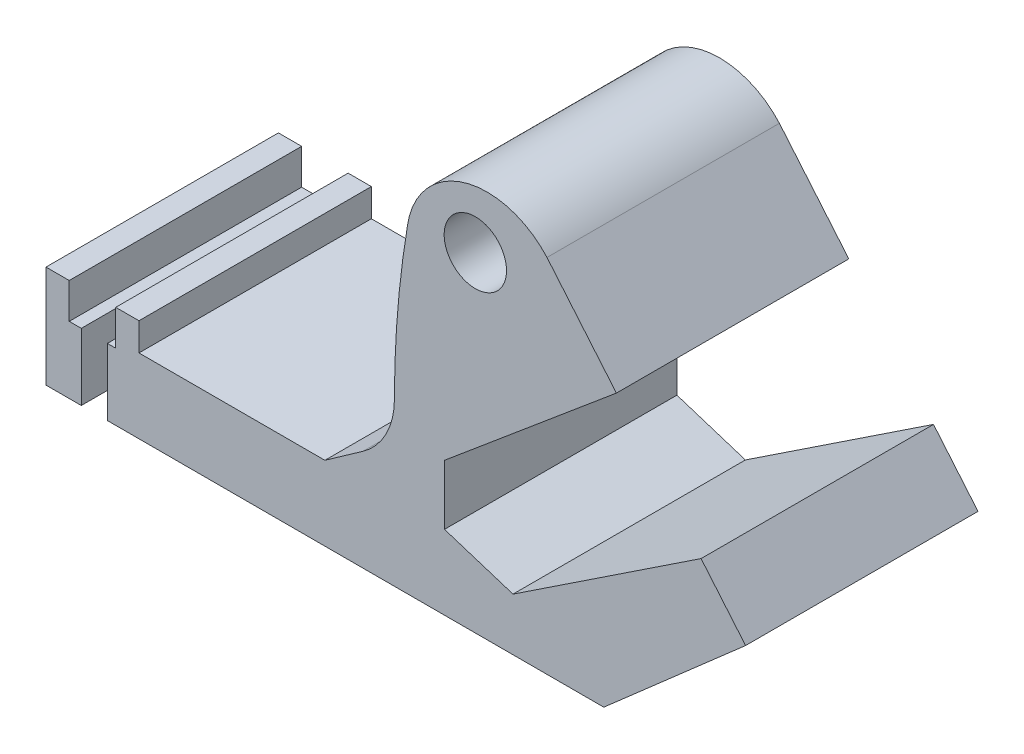
SolidWorks part; units mm, degrees
ref_plane "Front Plane" through (0, 0, 0) normal (0, 0, 1) x (1, 0, 0)
ref_plane "Top Plane" through (0, 0, 0) normal (0, 1, 0) x (1, 0, 0)
ref_plane "Right Plane" through (0, 0, 0) normal (1, 0, 0) x (0, 0, -1)
sketch "Sketch1" plane through (0, 0, 0) normal (0, 0, 1) x (1, 0, 0)
  line L0 (-80.137, 0) -> (39.863, 0)
  line L1 (-80.137, 0) -> (-80.137, 22)
  line L2 (-80.137, 22) -> (-75.137, 22)
  line L3 (-75.137, 22) -> (-75.137, 14.3836)
  line L4 (-75.137, 14.3836) -> (-65.137, 14.3836)
  line L5 (-65.137, 14.3836) -> (-65.137, 22)
  line L6 (-65.137, 22) -> (-60.137, 22)
  line L7 (-60.137, 22) -> (-60.137, 16)
  line L8 (-60.137, 16) -> (-20.137, 16)
  line L9 (-20.137, 16) -> (-11.9632, 21.7611)
  line L11 (42.5769, 59.8765) -> (5.5969, 28.8664)
  line L12 (5.5969, 28.8664) -> (5.5969, 16)
  line L13 (5.5969, 16) -> (20.3291, 11.2981)
  line L14 (20.3291, 11.2981) -> (60.7931, 38.1534)
  line L15 (60.7931, 38.1534) -> (70.3688, 26.7343)
  line L16 (70.3688, 26.7343) -> (39.863, 0)
  line L17 (42.5769, 59.8765) -> (27.6444, 77.6836)
  arc A0 (-11.9632, 21.7611) -> (-5.1809, 34.8391) centre (-21.1809, 34.8391) ccw
  arc A1 (-5.1809, 34.8391) -> (-2.3629, 68.6655) centre (199.2486, 34.8391) cw
  arc A3 (-2.3629, 68.6655) -> (28.3741, 76.8135) centre (14.7564, 66.1351) cw
  dimension "D8" = 16
  dimension "D1" = 120
  dimension "D2" = 22
  dimension "D3" = 5
  dimension "D4" = 10
  dimension "D5" = 5
  dimension "D6" = 6
  dimension "D7" = 10
extrude "Boss-Extrude1" add sketch "Sketch1" along normal blind 50 contours A3 A1 A0 L9 L8 L7 L6 L5 L4 L3 L2 L1 L0 L16 L15 L14 L13 L12 L11 L17
sketch "Sketch2" plane through (0, 0, 50) normal (0, 0, 1) x (1, 0, 0)
  circle A0 centre (12.231, 70.8694) radius 6.707
extrude "Cut-Extrude1" cut sketch "Sketch2" against normal blind 50
sketch "Sketch3" plane through (0, 0, 50) normal (0, 0, 1) x (1, 0, 0)
  line L0 (-75.137, 14.3836) -> (-65.137, 14.3836) construction
  line L1 (-72.5423, 14.3836) -> (-66.9264, 14.3836)
  line L2 (-72.5423, 14.3836) -> (-72.5423, -3.4745)
  line L3 (-72.5423, -3.4745) -> (-66.9264, -3.4745)
  line L4 (-66.9264, 14.3836) -> (-66.9264, -3.4745)
extrude "Cut-Extrude3" cut sketch "Sketch3" against normal blind 50
